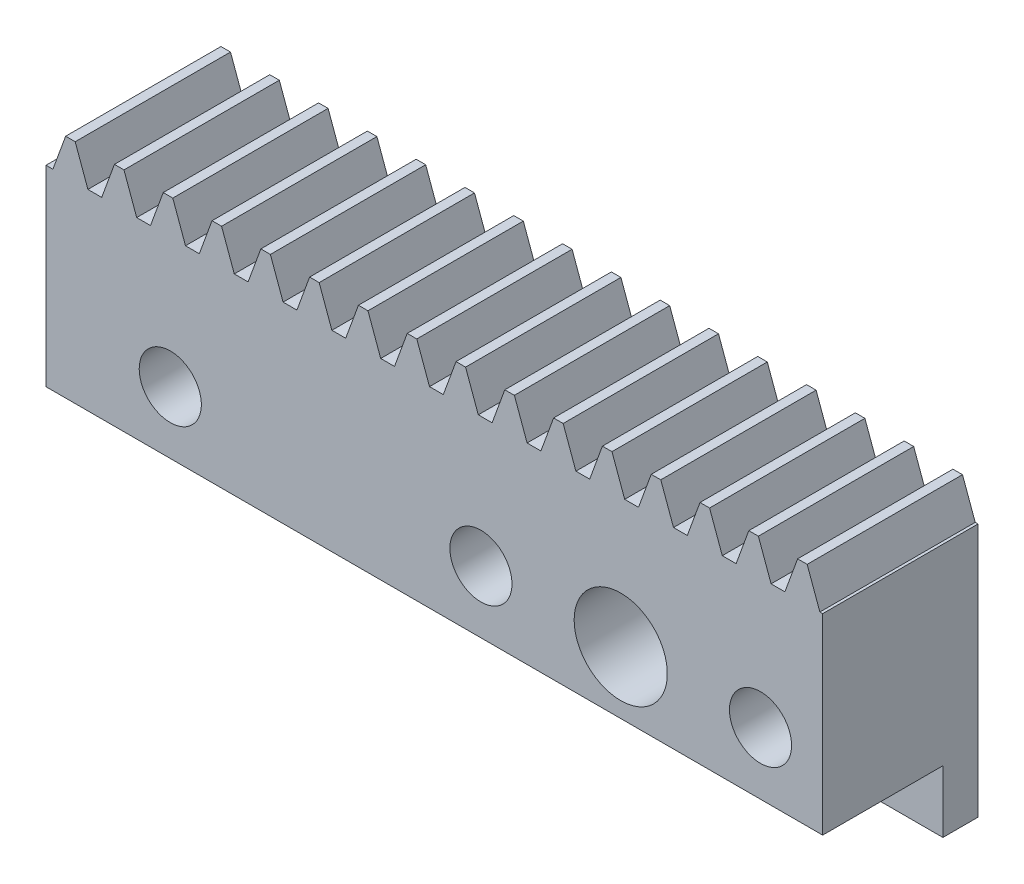
SolidWorks part; units mm, degrees
extrude "Blank" add sketch "BlankSke" against normal blind 4
sketch "BlankSke" plane through (0, 0, 0) normal (0, 0, 1) x (1, 0, 0)
  line L1 (0, 0) -> (25, 0)
  line L2 (0, 0) -> (0, 7.3)
  line L3 (0, 7.3) -> (25, 7.3)
  line L4 (25, 0) -> (25, 7.3)
  dimension "Length" = 25
  dimension "Blank_height" = 7.3
ref_plane "Plane1" through (0, 0, 0) normal (0, 0, 1) x (1, 0, 0)
ref_plane "Plane2" through (0, 0, 0) normal (0, 1, 0) x (1, 0, 0)
ref_plane "Plane3" through (0, 0, 0) normal (1, 0, 0) x (0, 0, -1)
sketch "HoldingSke" plane through (0, 0, 0) normal (0, 1, 0) x (1, 0, 0)
  line L0 (0, 0) -> (0.2783, 1.9805)
  line L1 (-15, 0) -> (100, 0) construction
  line L2 (0, 0) -> (-2.1039, 2.3779)
  line L3 (0, 0) -> (-11.863, 4.5341)
  line L4 (0, 0) -> (8.2587, 2.5249)
  line L5 (0, 0) -> (-23.7986, -8.8762)
  line L6 (0, 0) -> (-10.5278, -7.1032)
  line L9 (-71.009, 38.7566) -> (-47.5167, 47.3071)
  line L10 (-76.2, 2.8779) -> (-69.4, 2.8779)
  line L11 (0, 0) -> (-4, 0)
  line L12 (-76.2, 101.6) -> (-76.181, 101.6)
  line L13 (24.9733, 27.94) -> (52.9518, 28.4284)
  line L14 (24.9733, 27.94) -> (24.9743, 27.94)
  line L15 (24.9733, 27.94) -> (100.4006, 29.5858)
  circle A0 centre (0, 0) radius 19.05
  circle A1 centre (0, 0) radius 3.4
  circle A2 centre (0, 0) radius 12.7
  dimension "MPH" = 6.8
  dimension "Diameter" = 38.1
  dimension "Num_teeth" = 17
  dimension "Pitch" = 2
  dimension "Show_teeth" = 998
  dimension "Thickness" = 12.7
  dimension "Ap" = 20
  dimension "Pitch_height" = 6.8
  dimension "Width" = 4
  dimension "Backlash" = 0.019
  dimension "Addendum_fac" = 1
  dimension "Dedendum_fac" = 1.25
  dimension "Clearance_fac" = 0.25
  dimension "Dedendum_add" = 0.001
  dimension "Length" = 25
  dimension "Module" = 0.5
sketch "TooCutSkeIll" plane through (0, 0, 0) normal (0, 0, 1) x (1, 0, 0)
  line L0 (-0.6269, 7.2868) -> (-0.2524, 6.2579)
  line L1 (-0.134, 6.175) -> (0.134, 6.175)
  line L2 (0.2524, 6.2579) -> (0.6269, 7.2868)
  line L3 (25, 7.3) -> (0, 7.3) construction
  line L4 (0, 0) -> (0, 64.897) construction
  line L5 (-13.208, 6.8) -> (12.954, 6.8) construction
  line L6 (0, 0) -> (25, 0) construction
  line L7 (0.4497, 6.8) -> (0.4497, 48.7463) construction
  line L8 (-0.4497, 6.8) -> (-0.4497, 48.7463) construction
  line L9 (0.6457, 7.3) -> (0.6457, 7.3254)
  line L10 (-0.6457, 7.3) -> (-0.6457, 7.3254)
  line L11 (-0.6457, 7.3254) -> (0.6457, 7.3254)
  arc A0 (0.134, 6.175) -> (0.2524, 6.2579) centre (0.134, 6.301) ccw
  arc A1 (-0.2524, 6.2579) -> (-0.134, 6.175) centre (-0.134, 6.301) ccw
  arc A2 (0.6457, 7.3) -> (0.6269, 7.2868) centre (0.6457, 7.28) ccw
  arc A3 (-0.6269, 7.2868) -> (-0.6457, 7.3) centre (-0.6457, 7.28) ccw
  dimension "Pitch_height" = 6.8
  dimension "Addendum_plus" = 0.5254
  dimension "Pressure_angle" = 20
  dimension "Gap_width" = 0.8994
  dimension "Dedendum" = 0.625
extrude "ToothCutIll" [suppressed] cut sketch "TooCutSkeIll" against normal through all
sketch "TooCutSkeSim" plane through (0, 0, 0) normal (0, 0, 1) x (1, 0, 0)
  line L0 (0.2222, 6.175) -> (-0.2222, 6.175)
  line L1 (0.6409, 7.3254) -> (0.2222, 6.175)
  line L2 (0, 17.4625) -> (0, 53.467) construction
  line L3 (0.6409, 7.3254) -> (-0.6409, 7.3254)
  line L6 (-0.6409, 7.3254) -> (-0.2222, 6.175)
  line L9 (-0.4497, 6.8) -> (0.4497, 6.8) construction
  line L10 (0, 0) -> (25, 0) construction
  line L11 (0.4497, 6.8) -> (0.4497, 53.467) construction
  line L12 (-0.4497, 6.8) -> (-0.4497, 53.467) construction
  dimension "Pitch_height" = 6.8
  dimension "Addendum_plus" = 0.5254
  dimension "Pressure_angle" = 20
  dimension "Gap_width" = 0.8994
  dimension "Dedendum" = 0.625
extrude "ToothCutSim" cut sketch "TooCutSkeSim" against normal through all
pattern_linear "TeethCuts" count 17 spacing 1.5708 along (1, 0, 0) of "ToothCutIll", "ToothCutSim"
sketch "Sketch4" plane through (0, 0, 0) normal (0, -1, 0) x (1, 0, 0)
  line L0 (0, -50) -> (0, 50) construction
  line L1 (0, -4) -> (25, -4)
  line L2 (0, -4) -> (0, -2.87)
  line L3 (0, -2.87) -> (25, -2.87)
  line L4 (25, -4) -> (25, -2.87)
  line L5 (0, -4) -> (25, -4) construction
  line L6 (25, -4) -> (25, 0) construction
  dimension "D1" = 1.13
extrude "Boss-Extrude1" add sketch "Sketch4" along normal blind 2
sketch "Sketch7" plane through (0, 0, 0) normal (0, 0, 1) x (1, 0, 0)
  line L68 (25, 6.175) -> (24.9105, 6.175)
  line L69 (24.9105, 6.175) -> (24.5011, 7.3)
  line L70 (24.5011, 7.3) -> (24.1936, 7.3)
  line L71 (24.1936, 7.3) -> (23.7842, 6.175)
  line L72 (23.7842, 6.175) -> (23.3397, 6.175)
  line L73 (23.3397, 6.175) -> (22.9303, 7.3)
  line L74 (22.9303, 7.3) -> (22.6228, 7.3)
  line L75 (22.6228, 7.3) -> (22.2134, 6.175)
  line L76 (22.2134, 6.175) -> (21.7689, 6.175)
  line L77 (21.7689, 6.175) -> (21.3595, 7.3)
  line L78 (21.3595, 7.3) -> (21.052, 7.3)
  line L79 (21.052, 7.3) -> (20.6426, 6.175)
  line L80 (20.6426, 6.175) -> (20.1981, 6.175)
  line L81 (20.1981, 6.175) -> (19.7887, 7.3)
  line L82 (19.7887, 7.3) -> (19.4812, 7.3)
  line L83 (19.4812, 7.3) -> (19.0718, 6.175)
  line L84 (19.0718, 6.175) -> (18.6273, 6.175)
  line L85 (18.6273, 6.175) -> (18.2179, 7.3)
  line L86 (18.2179, 7.3) -> (17.9104, 7.3)
  line L87 (17.9104, 7.3) -> (17.501, 6.175)
  line L88 (17.501, 6.175) -> (17.0565, 6.175)
  line L89 (17.0565, 6.175) -> (16.6471, 7.3)
  line L90 (16.6471, 7.3) -> (16.3396, 7.3)
  line L91 (16.3396, 7.3) -> (15.9302, 6.175)
  line L92 (15.9302, 6.175) -> (15.4857, 6.175)
  line L93 (15.4857, 6.175) -> (15.0763, 7.3)
  line L94 (15.0763, 7.3) -> (14.7689, 7.3)
  line L95 (14.7689, 7.3) -> (14.3594, 6.175)
  line L96 (14.3594, 6.175) -> (13.9149, 6.175)
  line L97 (13.9149, 6.175) -> (13.5055, 7.3)
  line L98 (13.5055, 7.3) -> (13.1981, 7.3)
  line L99 (13.1981, 7.3) -> (12.7886, 6.175)
  line L100 (12.7886, 6.175) -> (12.3442, 6.175)
  line L101 (12.3442, 6.175) -> (11.9347, 7.3)
  line L102 (11.9347, 7.3) -> (11.6273, 7.3)
  line L103 (11.6273, 7.3) -> (11.2178, 6.175)
  line L104 (11.2178, 6.175) -> (10.7734, 6.175)
  line L105 (10.7734, 6.175) -> (10.3639, 7.3)
  line L106 (10.3639, 7.3) -> (10.0565, 7.3)
  line L107 (10.0565, 7.3) -> (9.647, 6.175)
  line L108 (9.647, 6.175) -> (9.2026, 6.175)
  line L109 (9.2026, 6.175) -> (8.7931, 7.3)
  line L110 (8.7931, 7.3) -> (8.4857, 7.3)
  line L111 (8.4857, 7.3) -> (8.0762, 6.175)
  line L112 (8.0762, 6.175) -> (7.6318, 6.175)
  line L113 (7.6318, 6.175) -> (7.2223, 7.3)
  line L114 (7.2223, 7.3) -> (6.9149, 7.3)
  line L115 (6.9149, 7.3) -> (6.5054, 6.175)
  line L116 (6.5054, 6.175) -> (6.061, 6.175)
  line L117 (6.061, 6.175) -> (5.6515, 7.3)
  line L118 (5.6515, 7.3) -> (5.3441, 7.3)
  line L119 (5.3441, 7.3) -> (4.9346, 6.175)
  line L120 (4.9346, 6.175) -> (4.4902, 6.175)
  line L121 (4.4902, 6.175) -> (4.0807, 7.3)
  line L122 (4.0807, 7.3) -> (3.7733, 7.3)
  line L123 (3.7733, 7.3) -> (3.3638, 6.175)
  line L124 (3.3638, 6.175) -> (2.9194, 6.175)
  line L125 (2.9194, 6.175) -> (2.5099, 7.3)
  line L126 (2.5099, 7.3) -> (2.2025, 7.3)
  line L127 (2.2025, 7.3) -> (1.793, 6.175)
  line L128 (1.793, 6.175) -> (1.3486, 6.175)
  line L129 (1.3486, 6.175) -> (0.9391, 7.3)
  line L130 (0.9391, 7.3) -> (0.6317, 7.3)
  line L131 (0.6317, 7.3) -> (0.2222, 6.175)
  line L132 (0.2222, 6.175) -> (0, 6.175)
  line L133 (0, 6.175) -> (0, 0)
  line L134 (0, 0) -> (25, 0)
  line L135 (25, 0) -> (25, 6.175)
  line L136 (25, 6.175) -> (24.9105, 6.175)
  line L137 (24.9105, 6.175) -> (24.5011, 7.3)
  line L138 (24.5011, 7.3) -> (24.1936, 7.3)
  line L139 (24.1936, 7.3) -> (23.7842, 6.175)
  line L140 (23.7842, 6.175) -> (23.3397, 6.175)
  line L141 (23.3397, 6.175) -> (22.9303, 7.3)
  line L142 (22.9303, 7.3) -> (22.6228, 7.3)
  line L143 (22.6228, 7.3) -> (22.2134, 6.175)
  line L144 (22.2134, 6.175) -> (21.7689, 6.175)
  line L145 (21.7689, 6.175) -> (21.3595, 7.3)
  line L146 (21.3595, 7.3) -> (21.052, 7.3)
  line L147 (21.052, 7.3) -> (20.6426, 6.175)
  line L148 (20.6426, 6.175) -> (20.1981, 6.175)
  line L149 (20.1981, 6.175) -> (19.7887, 7.3)
  line L150 (19.7887, 7.3) -> (19.4812, 7.3)
  line L151 (19.4812, 7.3) -> (19.0718, 6.175)
  line L152 (19.0718, 6.175) -> (18.6273, 6.175)
  line L153 (18.6273, 6.175) -> (18.2179, 7.3)
  line L154 (18.2179, 7.3) -> (17.9104, 7.3)
  line L155 (17.9104, 7.3) -> (17.501, 6.175)
  line L156 (17.501, 6.175) -> (17.0565, 6.175)
  line L157 (17.0565, 6.175) -> (16.6471, 7.3)
  line L158 (16.6471, 7.3) -> (16.3396, 7.3)
  line L159 (16.3396, 7.3) -> (15.9302, 6.175)
  line L160 (15.9302, 6.175) -> (15.4857, 6.175)
  line L161 (15.4857, 6.175) -> (15.0763, 7.3)
  line L162 (15.0763, 7.3) -> (14.7689, 7.3)
  line L163 (14.7689, 7.3) -> (14.3594, 6.175)
  line L164 (14.3594, 6.175) -> (13.9149, 6.175)
  line L165 (13.9149, 6.175) -> (13.5055, 7.3)
  line L166 (13.5055, 7.3) -> (13.1981, 7.3)
  line L167 (13.1981, 7.3) -> (12.7886, 6.175)
  line L168 (12.7886, 6.175) -> (12.3442, 6.175)
  line L169 (12.3442, 6.175) -> (11.9347, 7.3)
  line L170 (11.9347, 7.3) -> (11.6273, 7.3)
  line L171 (11.6273, 7.3) -> (11.2178, 6.175)
  line L172 (11.2178, 6.175) -> (10.7734, 6.175)
  line L173 (10.7734, 6.175) -> (10.3639, 7.3)
  line L174 (10.3639, 7.3) -> (10.0565, 7.3)
  line L175 (10.0565, 7.3) -> (9.647, 6.175)
  line L176 (9.647, 6.175) -> (9.2026, 6.175)
  line L177 (9.2026, 6.175) -> (8.7931, 7.3)
  line L178 (8.7931, 7.3) -> (8.4857, 7.3)
  line L179 (8.4857, 7.3) -> (8.0762, 6.175)
  line L180 (8.0762, 6.175) -> (7.6318, 6.175)
  line L181 (7.6318, 6.175) -> (7.2223, 7.3)
  line L182 (7.2223, 7.3) -> (6.9149, 7.3)
  line L183 (6.9149, 7.3) -> (6.5054, 6.175)
  line L184 (6.5054, 6.175) -> (6.061, 6.175)
  line L185 (6.061, 6.175) -> (5.6515, 7.3)
  line L186 (5.6515, 7.3) -> (5.3441, 7.3)
  line L187 (5.3441, 7.3) -> (4.9346, 6.175)
  line L188 (4.9346, 6.175) -> (4.4902, 6.175)
  line L189 (4.4902, 6.175) -> (4.0807, 7.3)
  line L190 (4.0807, 7.3) -> (3.7733, 7.3)
  line L191 (3.7733, 7.3) -> (3.3638, 6.175)
  line L192 (3.3638, 6.175) -> (2.9194, 6.175)
  line L193 (2.9194, 6.175) -> (2.5099, 7.3)
  line L194 (2.5099, 7.3) -> (2.2025, 7.3)
  line L195 (2.2025, 7.3) -> (1.793, 6.175)
  line L196 (1.793, 6.175) -> (1.3486, 6.175)
  line L197 (1.3486, 6.175) -> (0.9391, 7.3)
  line L198 (0.9391, 7.3) -> (0.6317, 7.3)
  line L199 (0.6317, 7.3) -> (0.2222, 6.175)
  line L200 (0.2222, 6.175) -> (0, 6.175)
  line L201 (0, 6.175) -> (0, 0)
  line L202 (0, 0) -> (25, 0)
  line L203 (25, 0) -> (25, 6.175)
  dimension "D1" = 0
extrude "Boss-Extrude2" add sketch "Sketch7" along normal blind 1
sketch "Sketch1" plane through (0, 0, -4) normal (0, 0, -1) x (-1, 0, 0)
  line L0 (-23, 2) -> (-25, 2)
  line L2 (-25, -2) -> (-25, 6.175) construction
  line L3 (-23, 0) -> (-23, 1)
  line L4 (0, 0) -> (-25, 0) construction
  line L5 (-23, 1) -> (-23, 3)
  line L6 (-22, 2) -> (-20, 2)
  line L7 (-20, 2) -> (-17, 2)
  line L8 (-17, 2) -> (-15, 2)
  line L9 (-15, 2) -> (-13, 2)
  line L10 (-13, 2) -> (-5, 2)
  line L11 (-5, 2) -> (-3, 2)
  circle A1 centre (-23, 2) radius 1
  circle A2 centre (-18.5, 2) radius 1.5
  circle A3 centre (-14, 2) radius 1
  circle A4 centre (-4, 2) radius 1
extrude "Cut-Extrude1" cut sketch "Sketch1" against normal through all contours L0 A1 L5 | A1 L5 | L5 A1 L0 | L7 A2 | L7 A2 | L9 A3 | L9 A3 | L11 A4 | L11 A4
equation "' \"Module@HoldingSke\" = 6.35"
equation "' \"Num_teeth@HoldingSke\" = 12"
equation "' \"Ap@HoldingSke\" =  20"
equation "' \"Ap@HoldingSke\" = 20"
equation "' \"Width@HoldingSke\" = 0.25 * 25.4"
equation "' \"Show_teeth@HoldingSke\" = 500"
equation "' \"Backlash@HoldingSke\" = 0.009 * 25.4"
equation "' \"Addendum_fac@HoldingSke\" = 1.0"
equation "' \"Dedendum_fac@HoldingSke\" = 1.25"
equation "' \"Dedendum_add@HoldingSke\" = 0.00005 * 25.4"
equation "' \"Clearance_fac@HoldingSke\" = 0.25"
equation "' \"Pitch_height@HoldingSke\" = 1 * 25.4"
equation "' \"Length@HoldingSke\" = 4.71 * 25.4"
equation "\"Pitch@HoldingSke\" = 1 / \"Module@HoldingSke\""
equation "\"MPH@HoldingSke\" = \"Dedendum_fac@HoldingSke\" / \"Pitch@HoldingSke\" + 2 * \"Dedendum_add@HoldingSke\" + 0.002 * 25.4"
equation "\"MPH@HoldingSke\" = ((sgn( \"MPH@HoldingSke\" - \"Pitch_height@HoldingSke\")+1)*( \"MPH@HoldingSke\" - \"Pitch_height@HoldingSke\"))/2 + \"Pitch_height@HoldingSke\""
equation "\"Blank_height@BlankSke\" = \"Pitch_height@HoldingSke\" + \"Addendum_fac@HoldingSke\"  / \"Pitch@HoldingSke\" "
equation "\"Length@BlankSke\" =  \"Length@HoldingSke\""
equation "\"Face_width@Blank\" = \"Width@HoldingSke\""
equation "\"Pressure_angle@TooCutSkeIll\" = \"Ap@HoldingSke\""
equation "\"Addendum_plus@TooCutSkeIll\" =  \"Addendum_fac@HoldingSke\"  / \"Pitch@HoldingSke\" + 0.001 *25.4"
equation "\"Dedendum@TooCutSkeIll\" = \"Dedendum_fac@HoldingSke\"  / \"Pitch@HoldingSke\""
equation "\"Pitch_height@TooCutSkeIll\" =  \"MPH@HoldingSke\""
equation "\"Gap_width@TooCutSkeIll\" = 3.14159265 / 2 / \"Pitch@HoldingSke\" + 6 * \"Backlash@HoldingSke\""
equation "\"Pressure_angle@TooCutSkeSim\" = \"Ap@HoldingSke\""
equation "\"Addendum_plus@TooCutSkeSim\" =  \"Addendum_fac@HoldingSke\"  / \"Pitch@HoldingSke\" + 0.001 * 25.4"
equation "\"Dedendum@TooCutSkeSim\" = \"Dedendum_fac@HoldingSke\"  / \"Pitch@HoldingSke\""
equation "\"Pitch_height@TooCutSkeSim\" =  \"MPH@HoldingSke\""
equation "\"Gap_width@TooCutSkeSim\" = 3.14159265 / 2 / \"Pitch@HoldingSke\" + 6 * \"Backlash@HoldingSke\""
equation "\"Root_fillet@TooCutSkeIll\" = \"Clearance_fac@HoldingSke\" / \"Pitch@HoldingSke\" + \"Dedendum_add@HoldingSke\""
equation "\"Break_rad@TooCutSkeIll\" = 0.02 / \"Pitch@HoldingSke\" * 2"
equation "\"Linear_pitch@TeethCuts\" = 3.14159265 / \"Pitch@HoldingSke\""
equation "\"Num_teeth@HoldingSke\" = int( ( \"Length@HoldingSke\" + 0 ) / (3.14159265 / \"Pitch@HoldingSke\")) + 0.9999  + 1"
equation " \"Num_teeth@TeethCuts\" = int( \"Show_teeth@HoldingSke\" ) + 1"
equation " \"Num_teeth@TeethCuts\" = ((sgn( \"Num_teeth@TeethCuts\" - \"Num_teeth@HoldingSke\" )-1)*( \"Num_teeth@TeethCuts\" - \"Num_teeth@HoldingSke\" ))/-2+ \"Num_teeth@HoldingSke\""
equation " \"Num_teeth@TeethCuts\" = ((sgn( \"Num_teeth@TeethCuts\" - 2.0)+1)*( \"Num_teeth@TeethCuts\" - 2.0))/2 +2.0"
